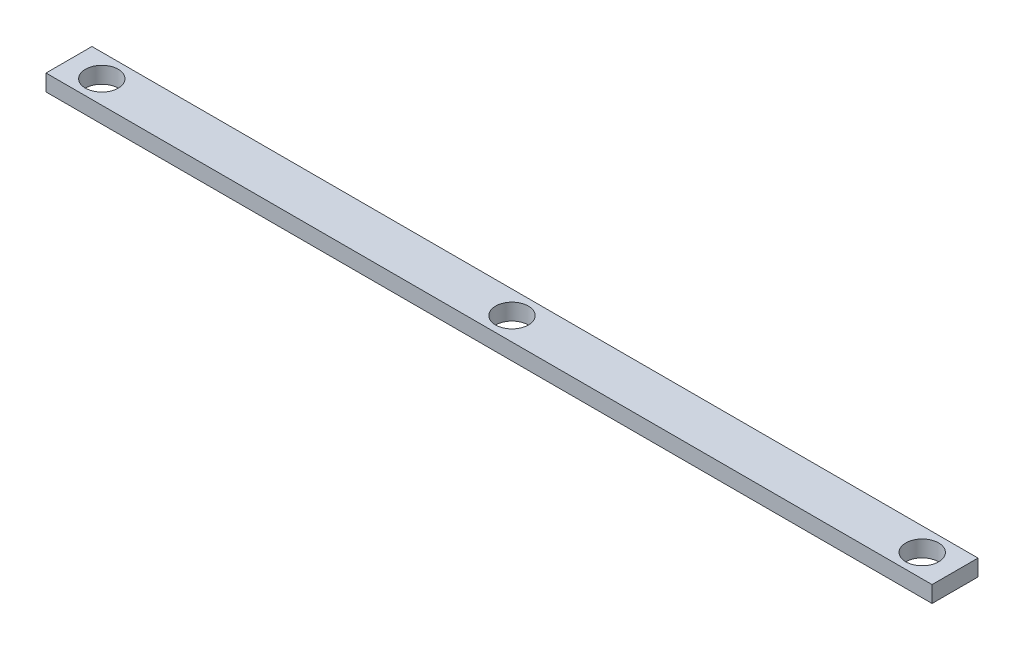
SolidWorks part; units mm, degrees
material "Plain Carbon Steel"
ref_plane "Front Plane" through (0, 0, 0) normal (0, 0, 1) x (1, 0, 0)
ref_plane "Top Plane" through (0, 0, 0) normal (0, 1, 0) x (1, 0, 0)
ref_plane "Right Plane" through (0, 0, 0) normal (1, 0, 0) x (0, 0, -1)
sketch "Sketch2" plane through (0, 0, 0) normal (0, 1, 0) x (0, 0, 1)
  line L1 (23002.9446, -12781.0305) -> (22862.9446, -12781.0305)
  line L2 (23002.9446, -12781.0305) -> (23002.9446, -10081.0305)
  line L3 (23002.9446, -10081.0305) -> (22862.9446, -10081.0305)
  line L4 (22862.9446, -12781.0305) -> (22862.9446, -10081.0305)
  circle A1 centre (22932.9446, -12681.0305) radius 50
  circle A2 centre (22932.9446, -11431.0305) radius 50
  circle A3 centre (22932.9446, -10181.0305) radius 50
extrude "Boss-Extrude1" add sketch "Sketch2" along normal blind 50
